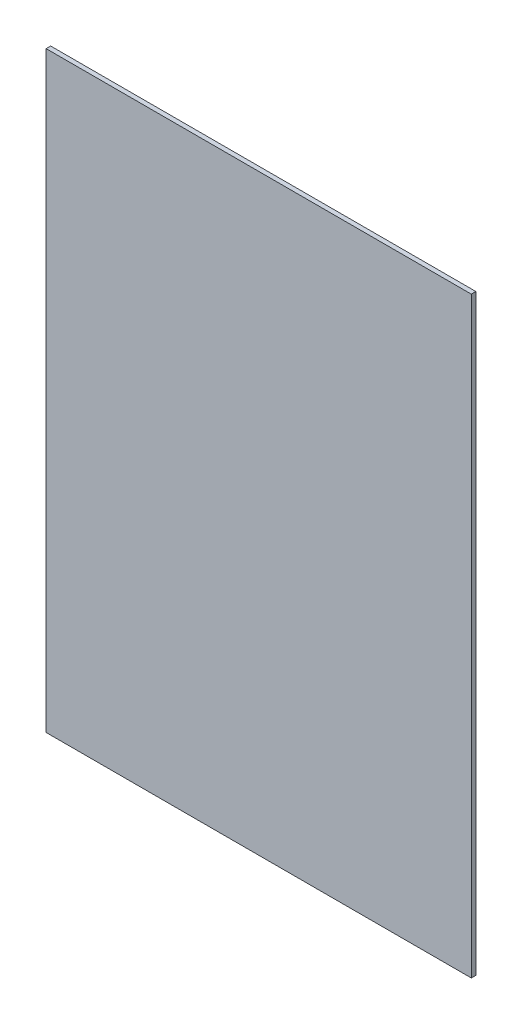
SolidWorks part; units mm, degrees
material "Cast Alloy Steel"
ref_plane "Front Plane" through (0, 0, 0) normal (0, 0, 1) x (1, 0, 0)
ref_plane "Top Plane" through (0, 0, 0) normal (0, 1, 0) x (1, 0, 0)
ref_plane "Right Plane" through (0, 0, 0) normal (1, 0, 0) x (0, 0, -1)
sketch "Sketch1" plane through (0, 0, 0) normal (0, 0, 1) x (1, 0, 0)
  line L0 (0, 0) -> (28, 0)
  line L1 (0, 0) -> (0, 39)
  line L2 (28, 0) -> (28, 39)
  line L3 (0, 39) -> (28, 39)
  dimension "D1" = 39
  dimension "D2" = 28
extrude "Boss-Extrude1" add sketch "Sketch1" along normal blind 0.3
